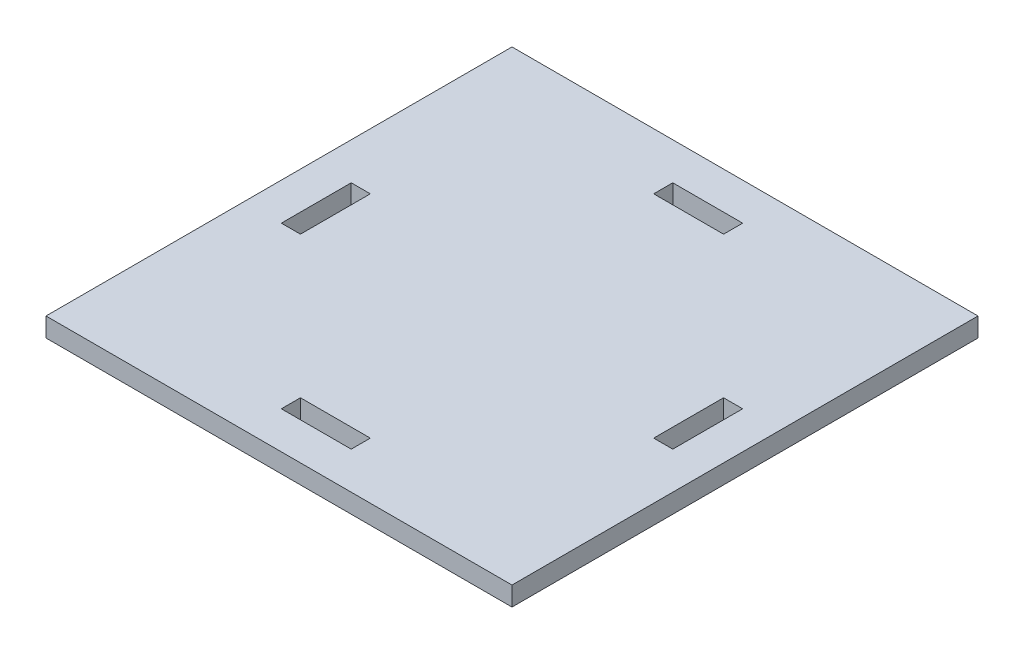
SolidWorks part; units mm, degrees
material "Corrugated Paper"
ref_plane "Front" through (0, 0, 0) normal (0, 0, 1) x (1, 0, 0)
ref_plane "Top" through (0, 0, 0) normal (0, 1, 0) x (1, 0, 0)
ref_plane "Right" through (0, 0, 0) normal (1, 0, 0) x (0, 0, -1)
sketch "Sketch1" plane through (0, 0, 0) normal (0, 1, 0) x (1, 0, 0)
  line L0 (50, 100) -> (50, 0) construction
  line L1 (0, 0) -> (100, 0)
  line L2 (0, 0) -> (0, 100)
  line L3 (0, 100) -> (100, 100)
  line L4 (100, 0) -> (100, 100)
  line L5 (0, 50) -> (100, 50) construction
  line L6 (42.5, 8) -> (42.5, 12.1)
  line L7 (42.5, 92) -> (57.5, 92)
  line L8 (42.5, 92) -> (42.5, 87.9)
  line L9 (42.5, 87.9) -> (57.5, 87.9)
  line L10 (57.5, 92) -> (57.5, 87.9)
  line L11 (57.5, 8) -> (57.5, 12.1)
  line L12 (42.5, 12.1) -> (57.5, 12.1)
  line L13 (42.5, 8) -> (57.5, 8)
  line L14 (42.5, 92) -> (0, 92) construction
  line L15 (57.5, 92) -> (100, 92) construction
  line L16 (0, 0) -> (100, 100) construction
  line L17 (8, 57.5) -> (12.1, 57.5)
  line L18 (8, 42.5) -> (8, 57.5)
  line L19 (8, 42.5) -> (12.1, 42.5)
  line L20 (12.1, 42.5) -> (12.1, 57.5)
  line L21 (92, 42.5) -> (87.9, 42.5)
  line L22 (92, 42.5) -> (92, 57.5)
  line L23 (87.9, 42.5) -> (87.9, 57.5)
  line L24 (92, 57.5) -> (87.9, 57.5)
  dimension "D1" = 100
  dimension "D2" = 84
  dimension "D3" = 4.1
  dimension "D4" = 15
extrude "Boss-Extrude1" add sketch "Sketch1" along normal blind 4.1
